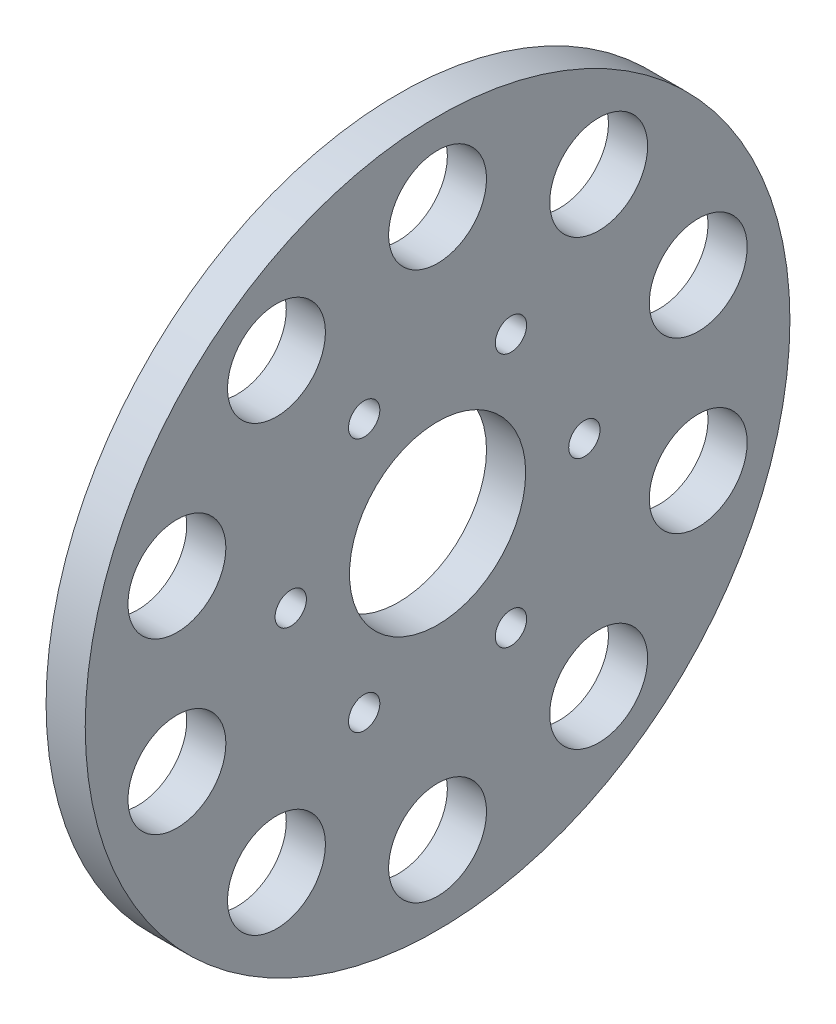
SolidWorks part; units mm, degrees
ref_plane "Front Plane" through (0, 0, 0) normal (0, 0, 1) x (1, 0, 0)
ref_plane "Top Plane" through (0, 0, 0) normal (0, 1, 0) x (1, 0, 0)
ref_plane "Right Plane" through (0, 0, 0) normal (1, 0, 0) x (0, 0, -1)
sketch "Sketch1" plane through (0, 0, 0) normal (1, 0, 0) x (0, 0, -1)
  line L0 (0, 0) -> (0, 44.45) construction
  circle A0 centre (0, 0) radius 14.2875
  circle A1 centre (0, 0) radius 57.15
  circle A2 centre (0, 44.45) radius 7.9375
  circle A3 centre (26.1271, 35.9608) radius 7.9375
  circle A4 centre (42.2745, 13.7358) radius 7.9375
  circle A5 centre (42.2745, -13.7358) radius 7.9375
  circle A6 centre (26.1271, -35.9608) radius 7.9375
  circle A7 centre (0, -44.45) radius 7.9375
  circle A8 centre (-26.1271, -35.9608) radius 7.9375
  circle A9 centre (-42.2745, -13.7358) radius 7.9375
  circle A10 centre (-42.2745, 13.7358) radius 7.9375
  circle A11 centre (-26.1271, 35.9608) radius 7.9375
  point P16 (0, 0)
  dimension "D1" = 44.45
  dimension "D2" = 15.875
  dimension "D4" = 114.3
  dimension "D5" = 28.575
  dimension "D3" = 10
extrude "Boss-Extrude1" add sketch "Sketch1" along normal blind 6.35
sketch "Sketch3" plane through (6.35, 0, 0) normal (1, 0, 0) x (0, 0, -1)
  line L0 (0, 0) -> (0, 57.15) construction
  circle A0 centre (0, 0) radius 57.15 construction
sketch "Sketch4" plane through (0, 0, 0) normal (-1, 0, 0) x (0, 0, 1)
  circle A0 centre (-11.9063, -20.6222) radius 2.54 construction
  circle A1 centre (-23.8125, 0) radius 2.54 construction
  circle A2 centre (-11.9062, 20.6222) radius 2.54 construction
  circle A3 centre (11.9063, 20.6222) radius 2.54 construction
  circle A4 centre (23.8125, 0) radius 2.54 construction
  circle A5 centre (11.9062, -20.6222) radius 2.54 construction
  circle A6 centre (-11.9063, -20.6222) radius 2.54
  circle A7 centre (-23.8125, 0) radius 2.54
  circle A8 centre (-11.9062, 20.6222) radius 2.54
  circle A9 centre (11.9063, 20.6222) radius 2.54
  circle A10 centre (23.8125, 0) radius 2.54
  circle A11 centre (11.9062, -20.6222) radius 2.54
extrude "Cut-Extrude1" cut sketch "Sketch4" against normal up to next
